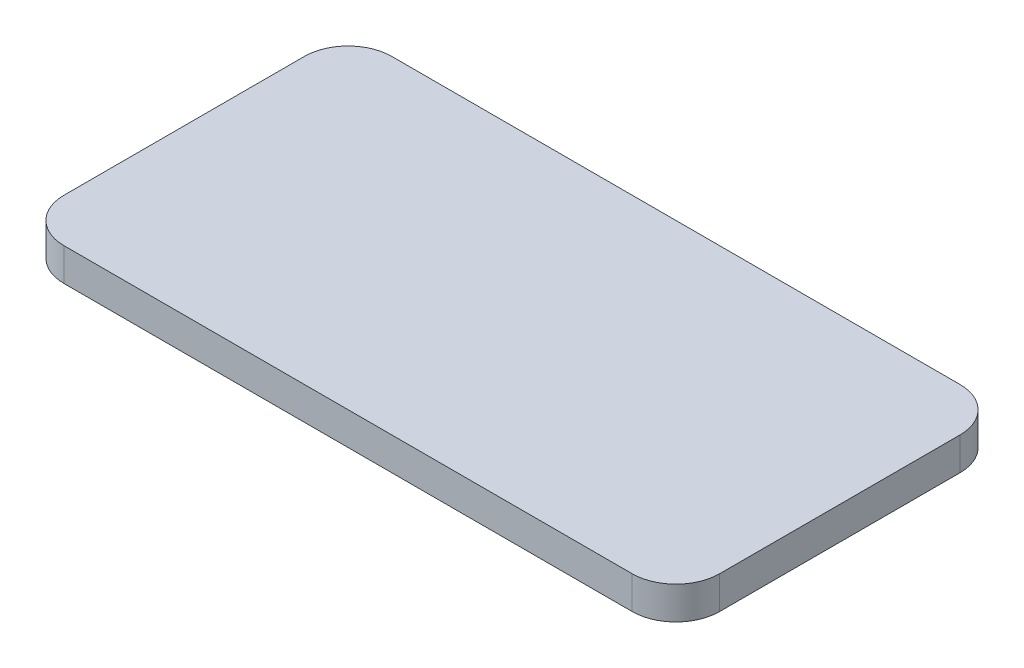
SolidWorks part; units mm, degrees
ref_plane "前视基准面" through (0, 0, 0) normal (0, 0, 1) x (1, 0, 0)
ref_plane "上视基准面" through (0, 0, 0) normal (0, 1, 0) x (1, 0, 0)
ref_plane "右视基准面" through (0, 0, 0) normal (1, 0, 0) x (0, 0, -1)
other "Configuration Table"
sketch "草图1" plane through (0, 0, 0) normal (0, 1, 0) x (1, 0, 0)
  line L1 (-13, -7.5) -> (13, -7.5)
  line L2 (-15, -5.5) -> (-15, 5.5)
  line L3 (-13, 7.5) -> (13, 7.5)
  line L4 (15, -5.5) -> (15, 5.5)
  line L5 (-15, -7.5) -> (15, 7.5) construction
  line L6 (-15, 7.5) -> (15, -7.5) construction
  arc A0 (-13, -7.5) -> (-15, -5.5) centre (-13, -5.5) cw
  arc A1 (13, -7.5) -> (15, -5.5) centre (13, -5.5) ccw
  arc A2 (13, 7.5) -> (15, 5.5) centre (13, 5.5) cw
  arc A3 (-15, 5.5) -> (-13, 7.5) centre (-13, 5.5) cw
  point P0 (0, 0)
  point P6 (0, 0)
  dimension "D3" = 2
  dimension "D1" = 15
  dimension "D2" = 30
extrude "凸台-拉伸1" add sketch "草图1" along normal blind 1.5
